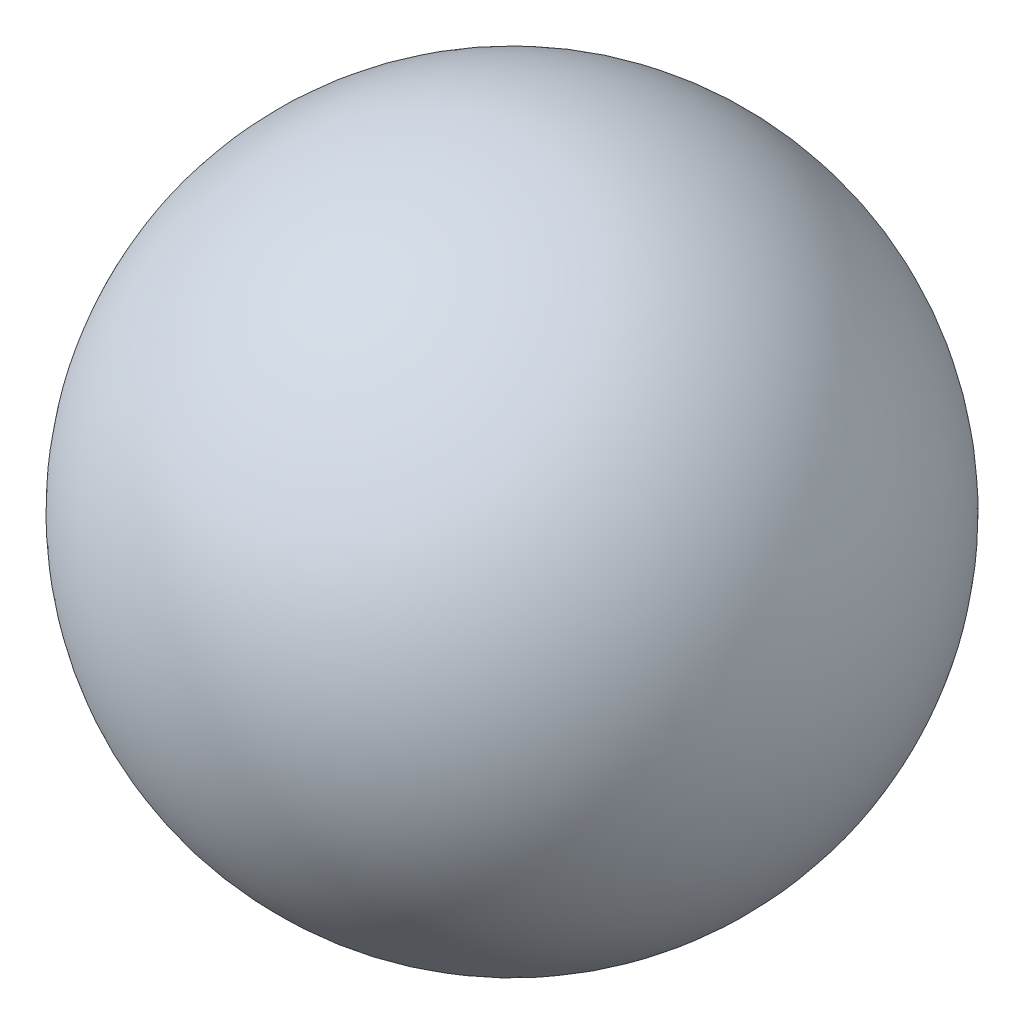
SolidWorks part; units mm, degrees
ref_plane "Front Plane" through (0, 0, 0) normal (0, 0, 1) x (1, 0, 0)
ref_plane "Top Plane" through (0, 0, 0) normal (0, 1, 0) x (1, 0, 0)
ref_plane "Right Plane" through (0, 0, 0) normal (1, 0, 0) x (0, 0, -1)
sketch "Sketch1" plane through (0, 0, 0) normal (0, 1, 0) x (1, 0, 0)
  line L0 (-63.5, 0) -> (63.5, 0)
  arc A0 (63.5, 0) -> (-63.5, 0) centre (0, 0) ccw
  dimension "D1" = 127
revolve "Revolve1" add sketch "Sketch1" angle 360 about L0
sketch "Sketch2" plane through (0, 0, 0) normal (0, 0, 1) x (1, 0, 0)
  line L1 (-63.5, 63.5) -> (63.5, 63.5)
  line L2 (-63.5, 63.5) -> (-63.5, -63.5)
  line L3 (-63.5, -63.5) -> (63.5, -63.5)
  line L4 (63.5, 63.5) -> (63.5, -63.5)
  dimension "D1" = 127
sketch "Sketch3" plane through (0, 0, 0) normal (0, 1, 0) x (1, 0, 0)
  line L1 (63.5, 63.5) -> (-63.5, 63.5)
  line L2 (63.5, 63.5) -> (63.5, -63.5)
  line L3 (63.5, -63.5) -> (-63.5, -63.5)
  line L4 (-63.5, 63.5) -> (-63.5, -63.5)
  dimension "D1" = 127
sketch "Sketch4" plane through (0, 0, 0) normal (1, 0, 0) x (0, 0, -1)
  line L1 (63.5, 63.5) -> (-63.5, 63.5)
  line L2 (63.5, 63.5) -> (63.5, -63.5)
  line L3 (63.5, -63.5) -> (-63.5, -63.5)
  line L4 (-63.5, 63.5) -> (-63.5, -63.5)
  dimension "D1" = 127
ref_plane "Mid_Plane" through (0, 0, 0) normal (1, 0, 0) x (0, 0, -1)
